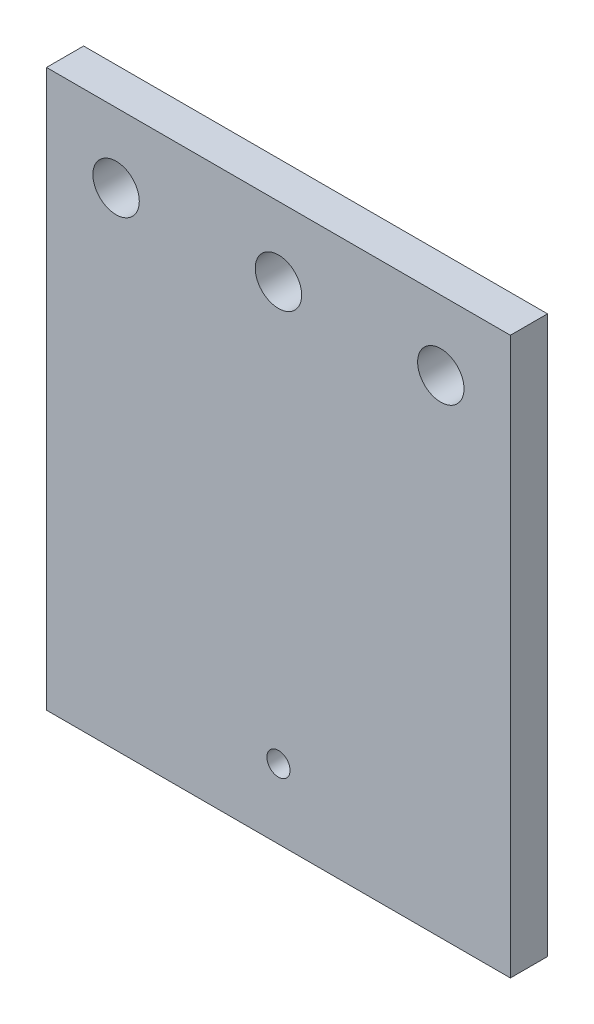
SolidWorks part; units mm, degrees
material "Hexcel AS4C (3000 Filaments)"
ref_plane "Front Plane" through (0, 0, 0) normal (0, 0, 1) x (1, 0, 0)
ref_plane "Top Plane" through (0, 0, 0) normal (0, 1, 0) x (1, 0, 0)
ref_plane "Right Plane" through (0, 0, 0) normal (1, 0, 0) x (0, 0, -1)
sketch "Sketch1" plane through (0, 0, 0) normal (0, 0, 1) x (1, 0, 0)
  line L0 (63.5, 0) -> (63.5, 152.4) construction
  line L1 (0, 0) -> (127, 0)
  line L2 (0, 0) -> (0, 152.4)
  line L3 (0, 152.4) -> (127, 152.4)
  line L4 (127, 0) -> (127, 152.4)
  line L5 (0, 19.05) -> (127, 19.05) construction
  line L6 (0, 133.35) -> (127, 133.35) construction
  circle A0 centre (63.5, 19.05) radius 3.175
  circle A1 centre (19.05, 133.35) radius 6.35
  circle A2 centre (63.5, 133.35) radius 6.35
  circle A3 centre (107.95, 133.35) radius 6.35
  point P19 (0, 0)
  point P20 (0, 0)
  dimension "D3" = 6.35
  dimension "D8" = 12.7
  dimension "D1" = 127
  dimension "D2" = 152.4
  dimension "D4" = 19.05
  dimension "D5" = 19.05
  dimension "D6" = 44.45
  dimension "D7" = 44.45
extrude "Boss-Extrude1" add sketch "Sketch1" along normal blind 10.16
